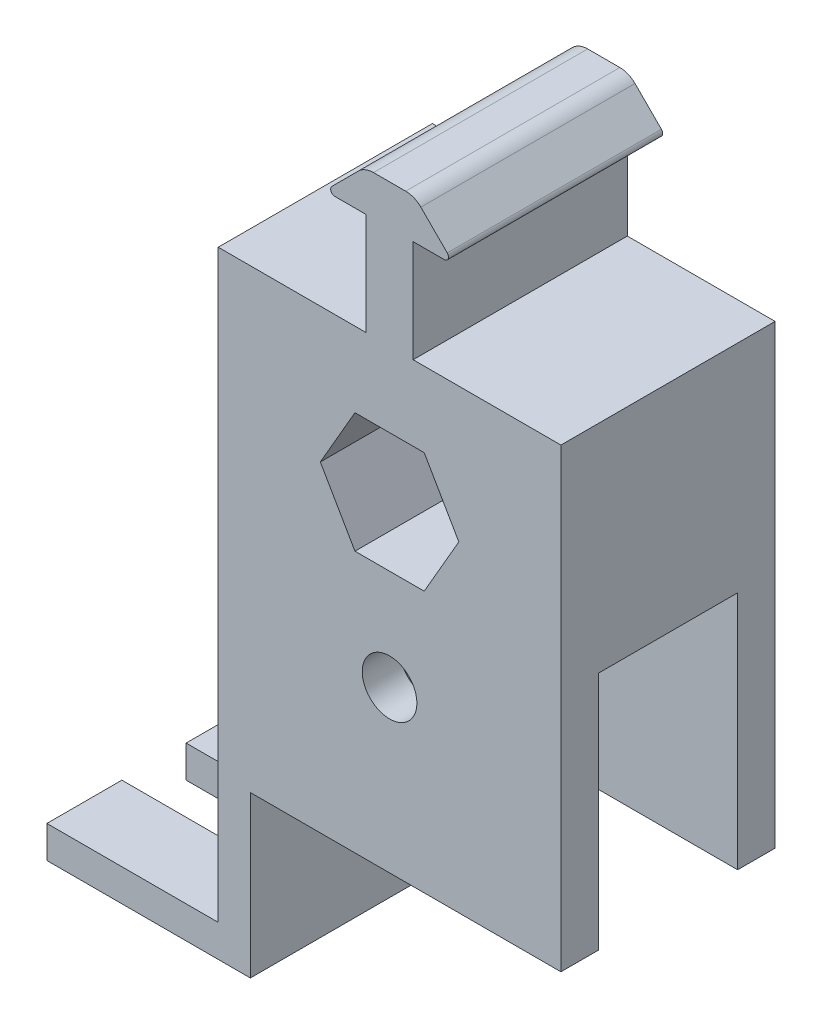
SolidWorks part; units mm, degrees
ref_plane "Front Plane" through (0, 0, 0) normal (0, 0, 1) x (1, 0, 0)
ref_plane "Top Plane" through (0, 0, 0) normal (0, 1, 0) x (1, 0, 0)
ref_plane "Right Plane" through (0, 0, 0) normal (1, 0, 0) x (0, 0, -1)
sketch "Sketch1" plane through (0, 0, 0) normal (0, 0, 1) x (1, 0, 0)
  line L0 (-20.32, 16.002) -> (-20.32, -38.1)
  line L1 (-4.1061, 7.112) -> (-8.2122, 0)
  line L2 (-8.2122, 0) -> (-4.1061, -7.112)
  line L3 (-4.1061, -7.112) -> (4.1061, -7.112)
  line L4 (4.1061, -7.112) -> (8.2122, 0)
  line L5 (8.2122, 0) -> (4.1061, 7.112)
  line L6 (4.1061, 7.112) -> (-4.1061, 7.112)
  line L7 (-20.32, -38.1) -> (20.32, -38.1)
  line L8 (20.32, -38.1) -> (20.32, 16.002)
  line L9 (-20.32, 16.002) -> (-2.794, 16.002)
  line L10 (-2.794, 16.002) -> (-2.794, 28.1305)
  line L11 (-2.794, 28.1305) -> (-6.477, 28.1305)
  line L12 (-6.8362, 28.9977) -> (-3.7065, 32.1275)
  line L13 (-1.9104, 32.8714) -> (1.9104, 32.8714)
  line L14 (0, 41.8096) -> (0, -25.778) construction
  line L15 (20.32, 16.002) -> (2.794, 16.002)
  line L16 (2.794, 16.002) -> (2.794, 28.1305)
  line L17 (6.8362, 28.9977) -> (3.7065, 32.1275)
  line L18 (2.794, 28.1305) -> (6.477, 28.1305)
  line L19 (-6.985, 28.6385) -> (6.985, 28.6385) construction
  circle A0 centre (0, 0) radius 7.112 construction
  arc A1 (-6.477, 28.1305) -> (-6.8362, 28.9977) centre (-6.477, 28.6385) cw
  arc A2 (-3.7065, 32.1275) -> (-1.9104, 32.8714) centre (-1.9104, 30.3314) cw
  arc A3 (3.7065, 32.1275) -> (1.9104, 32.8714) centre (1.9104, 30.3314) ccw
  arc A4 (6.477, 28.1305) -> (6.8362, 28.9977) centre (6.477, 28.6385) ccw
  point P18 (7.7034, 28.1305)
  point P21 (-4.6355, 28.1305)
  point P25 (-7.7034, 28.1305)
  point P29 (0, -38.1)
  point P35 (0, 32.8714)
  dimension "D7" = 0.508
  dimension "D8" = 2.54
  dimension "D1" = 14.224
  dimension "D2" = 21.0185
  dimension "D3" = 5.588
  dimension "D4" = 4.7409
  dimension "D5" = 135
  dimension "D6" = 13.97
  dimension "D9" = 38.1
  dimension "D10" = 8.89
  dimension "D11" = 20.32
extrude "Boss-Extrude1" add sketch "Sketch1" along normal mid plane 25.4
sketch "Sketch10" plane through (0, 0, 0) normal (0, 0, 1) x (1, 0, 0)
  line L0 (-20.32, -38.1) -> (-20.32, -53.34)
  line L1 (-20.32, -53.34) -> (-40.64, -53.34)
  line L2 (-40.64, -53.34) -> (-40.64, -57.15)
  line L3 (-40.64, -57.15) -> (-16.51, -57.15)
  line L4 (-16.51, -57.15) -> (-16.51, -38.1)
  line L5 (-20.32, -38.1) -> (20.32, -38.1) construction
  line L6 (-20.32, -38.1) -> (-16.51, -38.1)
  dimension "D2" = 15.24
  dimension "D3" = 3.81
  dimension "D4" = 20.32
extrude "Boss-Extrude4" add sketch "Sketch10" along normal up to surface and the other way up to surface up to face at (0, 18.0275, 12.7) other way up to face at (0, 18.0275, -12.7)
sketch "Sketch6" plane through (20.32, 0, 0) normal (1, 0, 0) x (0, 0, -1)
  line L0 (-12.7, -7.112) -> (12.7, -7.112) construction
  line L1 (-12.7, -7.112) -> (12.7, -7.112) construction
  line L2 (-8.255, -25.4) -> (-8.255, -9.652)
  line L3 (-8.255, -9.652) -> (8.255, -9.652)
  line L11 (-8.255, -25.4) -> (8.255, -25.4)
  line L12 (8.255, -9.652) -> (8.255, -25.4)
  point P10 (0, -9.652)
  dimension "D2" = 16.51
  dimension "D3" = 2.54
  dimension "D1" = 15.748
extrude "Cut-Extrude2" cut sketch "Sketch6" against normal through all
sketch "Sketch11" plane through (0, -53.34, 0) normal (0, 1, 0) x (1, 0, 0)
  line L0 (-40.64, -12.7) -> (-40.64, 12.7) construction
  line L1 (-20.32, -12.7) -> (-20.32, 12.7) construction
  line L2 (-40.64, -3.81) -> (-40.64, 3.81)
  line L3 (-20.32, -3.81) -> (-20.32, 3.81)
  line L4 (-40.64, 3.81) -> (-20.32, 3.81)
  line L5 (-40.64, -3.81) -> (-20.32, -3.81)
  point P8 (-20.32, 0)
  point P9 (-40.64, 0)
  dimension "D1" = 7.62
extrude "Cut-Extrude3" cut sketch "Sketch11" against normal up to surface (3.81 mm away) up to face at (-28.575, -57.15, 0)
sketch "Sketch15" plane through (0, 0, 12.7) normal (0, 0, 1) x (1, 0, 0)
  line L1 (-4.1061, -7.112) -> (4.1061, -7.112) construction
  circle A0 centre (0, -19.05) radius 3.2385
  point P7 (0, -7.112)
  dimension "D1" = 6.477
  dimension "D2" = 11.938
extrude "Cut-Extrude4" cut sketch "Sketch15" against normal up to surface (25.4 mm away) up to face at (-5.715, 3.373, -12.7)
sketch "Sketch16" plane through (20.32, 0, 0) normal (1, 0, 0) x (0, 0, -1)
  line L0 (-8.255, -25.4) -> (8.255, -25.4) construction
  line L1 (-8.255, -25.4) -> (8.255, -25.4)
  line L2 (-8.255, -25.4) -> (-8.255, -38.1)
  line L3 (-12.7, -38.1) -> (12.7, -38.1) construction
  line L4 (-8.255, -38.1) -> (8.255, -38.1)
  line L5 (8.255, -38.1) -> (8.255, -25.4)
extrude "Cut-Extrude5" cut sketch "Sketch16" against normal up to surface (36.83 mm away) up to face at (-16.51, -47.625, 0)
